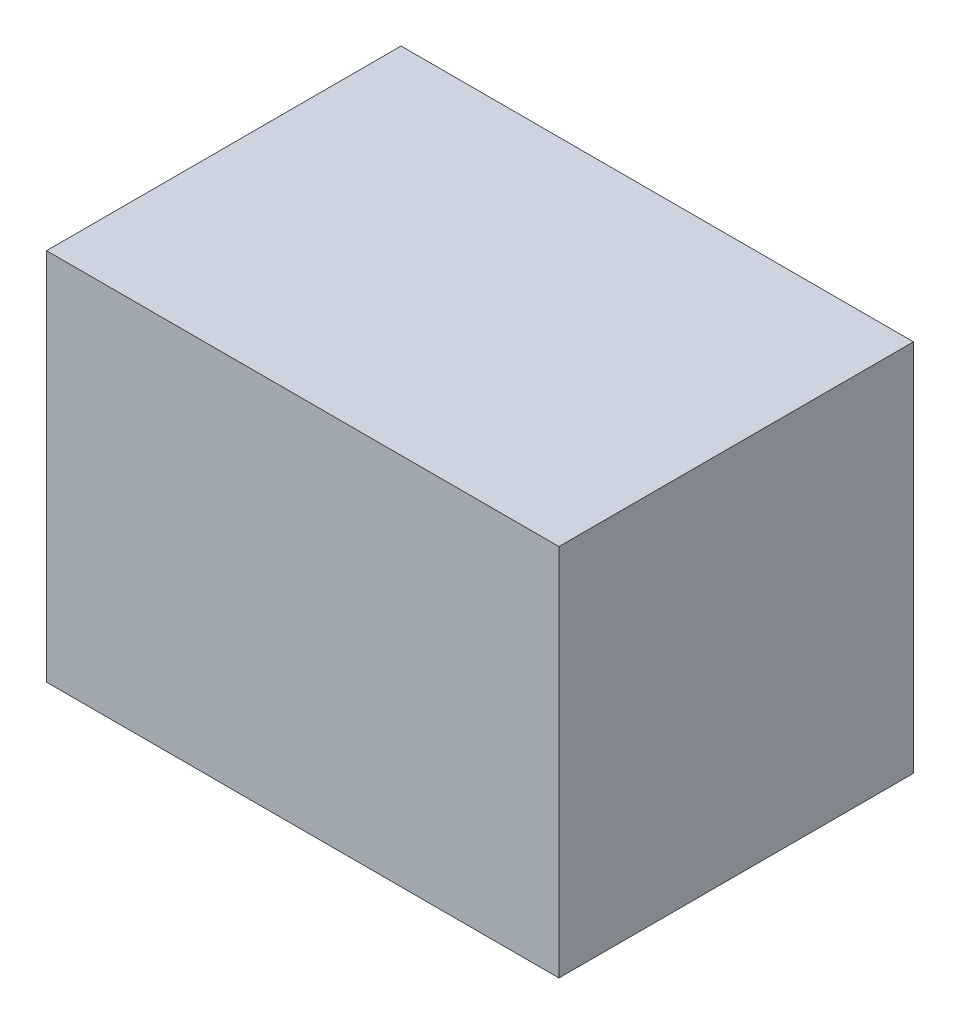
SolidWorks part; units mm, degrees
material "Balsa"
ref_plane "Front Plane" through (0, 0, 0) normal (0, 0, 1) x (1, 0, 0)
ref_plane "Top Plane" through (0, 0, 0) normal (0, 1, 0) x (1, 0, 0)
ref_plane "Right Plane" through (0, 0, 0) normal (1, 0, 0) x (0, 0, -1)
sketch "Sketch1" plane through (0, 0, 0) normal (0, 1, 0) x (1, 0, 0)
  line L1 (-24, -16.6045) -> (24, -16.6045)
  line L2 (-24, -16.6045) -> (-24, 16.6045)
  line L3 (-24, 16.6045) -> (24, 16.6045)
  line L4 (24, -16.6045) -> (24, 16.6045)
  line L5 (-24, -16.6045) -> (24, 16.6045) construction
  line L6 (-24, 16.6045) -> (24, -16.6045) construction
  point P0 (0, 0)
  dimension "D1" = 48
  dimension "D2" = 33.209
extrude "Boss-Extrude1" add sketch "Sketch1" along normal blind 35
